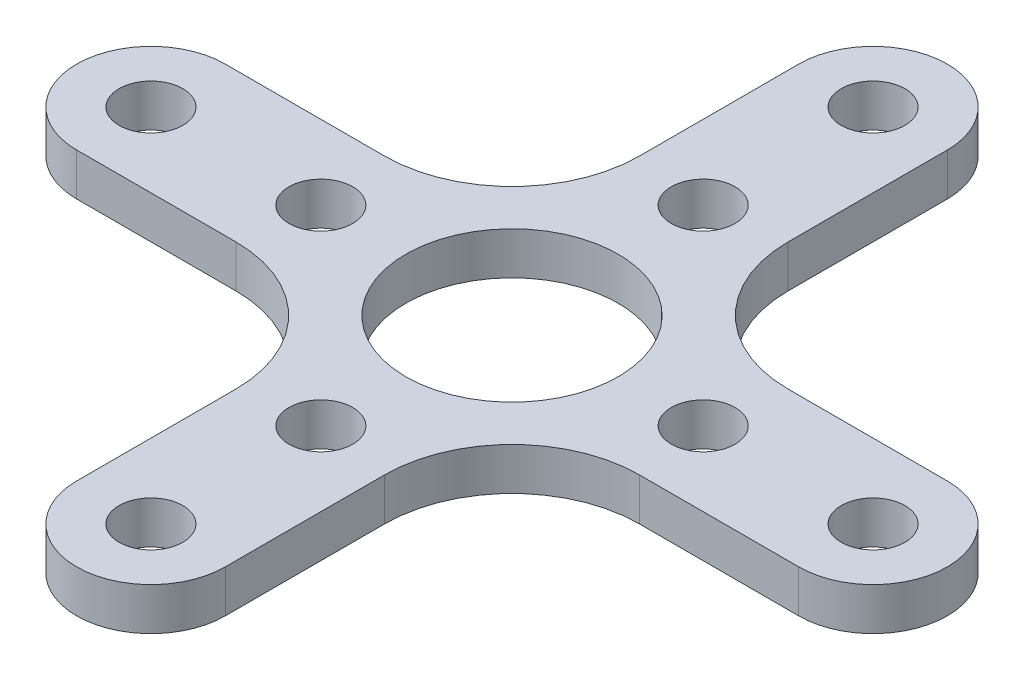
SolidWorks part; units mm, degrees
ref_plane "Front Plane" through (0, 0, 0) normal (0, 0, 1) x (1, 0, 0)
ref_plane "Top Plane" through (0, 0, 0) normal (0, 1, 0) x (1, 0, 0)
ref_plane "Right Plane" through (0, 0, 0) normal (1, 0, 0) x (0, 0, -1)
sketch "Sketch1" plane through (0, 0, 0) normal (0, 1, 0) x (1, 0, 0)
  line L0 (0, -20.5) -> (0, 20.5) construction
  line L1 (-20.5, 0) -> (20.5, 0) construction
  line L2 (-17, 3.5) -> (-3.5, 3.5) construction
  line L3 (-3.5, 3.5) -> (-3.5, 17) construction
  line L4 (3.5, 17) -> (3.5, 3.5) construction
  line L5 (3.5, 3.5) -> (17, 3.5) construction
  line L6 (3.5, -3.5) -> (17, -3.5) construction
  line L7 (3.5, -17) -> (3.5, -3.5) construction
  line L8 (-3.5, -3.5) -> (-3.5, -17) construction
  line L9 (-17, -3.5) -> (-3.5, -3.5) construction
  line L10 (-3.5, 17) -> (-3.5, 9.5)
  line L11 (3.5, 17) -> (3.5, 9.5)
  line L12 (9.5, 3.5) -> (17, 3.5)
  line L13 (17, -3.5) -> (9.5, -3.5)
  line L14 (3.5, -9.5) -> (3.5, -17)
  line L15 (-3.5, -17) -> (-3.5, -9.5)
  line L16 (-9.5, -3.5) -> (-17, -3.5)
  line L17 (-17, 3.5) -> (-9.5, 3.5)
  arc A1 (-3.5, 17) -> (3.5, 17) centre (0, 17) cw
  arc A2 (-3.5, -17) -> (3.5, -17) centre (0, -17) ccw
  arc A3 (-17, 3.5) -> (-17, -3.5) centre (-17, 0) ccw
  arc A4 (17, 3.5) -> (17, -3.5) centre (17, 0) cw
  arc A5 (-9.5, 3.5) -> (-3.5, 9.5) centre (-9.5, 9.5) ccw
  arc A6 (3.5, 9.5) -> (9.5, 3.5) centre (9.5, 9.5) ccw
  arc A7 (9.5, -3.5) -> (3.5, -9.5) centre (9.5, -9.5) ccw
  arc A8 (-3.5, -9.5) -> (-9.5, -3.5) centre (-9.5, -9.5) ccw
  point P4 (-9.5, 3.5)
  point P11 (-3.5, 9.5)
  point P38 (0, 0)
  dimension "D1" = 41
  dimension "D2" = 41
  dimension "D3" = 3.5
  dimension "D4" = 3.5
  dimension "D5" = 11
  dimension "D6" = 11
  dimension "D7" = 4
extrude "Boss-Extrude1" add sketch "Sketch1" along normal blind 2
sketch "Sketch2" plane through (0, 2, 0) normal (0, 1, 0) x (1, 0, 0)
  circle A0 centre (0, 17) radius 1.5
  circle A1 centre (0, 9) radius 1.5
  circle A2 centre (0, 0) radius 5
  circle A3 centre (17, 0) radius 1.5
  circle A4 centre (9, 0) radius 1.5
  circle A5 centre (0, -17) radius 1.5
  circle A6 centre (0, -9) radius 1.5
  circle A7 centre (-17, 0) radius 1.5
  circle A8 centre (-9, 0) radius 1.5
  point P22 (0, 0)
  dimension "D1" = 3
  dimension "D2" = 3
  dimension "D3" = 10
  dimension "D4" = 9
  dimension "D5" = 17
  dimension "D6" = 4
extrude "Cut-Extrude1" cut sketch "Sketch2" against normal blind 2
